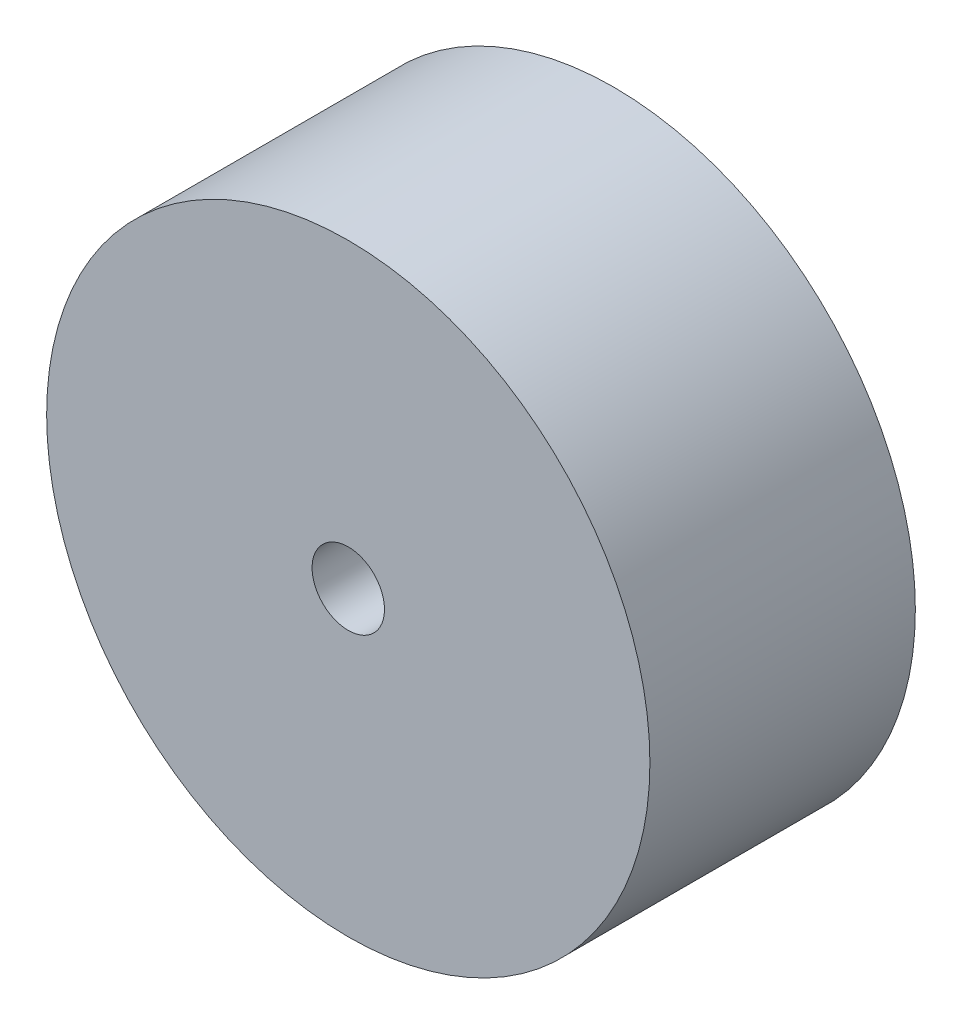
SolidWorks part; units mm, degrees
ref_plane "前视基准面" through (0, 0, 0) normal (0, 0, 1) x (1, 0, 0)
ref_plane "上视基准面" through (0, 0, 0) normal (0, 1, 0) x (1, 0, 0)
ref_plane "右视基准面" through (0, 0, 0) normal (1, 0, 0) x (0, 0, -1)
sketch "草图1" plane through (0, 0, 0) normal (0, 0, 1) x (1, 0, 0)
  circle A0 centre (0, 0) radius 0.6
  circle A1 centre (0, 0) radius 5
  dimension "D1" = 10
  dimension "D2" = 1.2
extrude "凸台-拉伸1" add sketch "草图1" along normal blind 4.4
